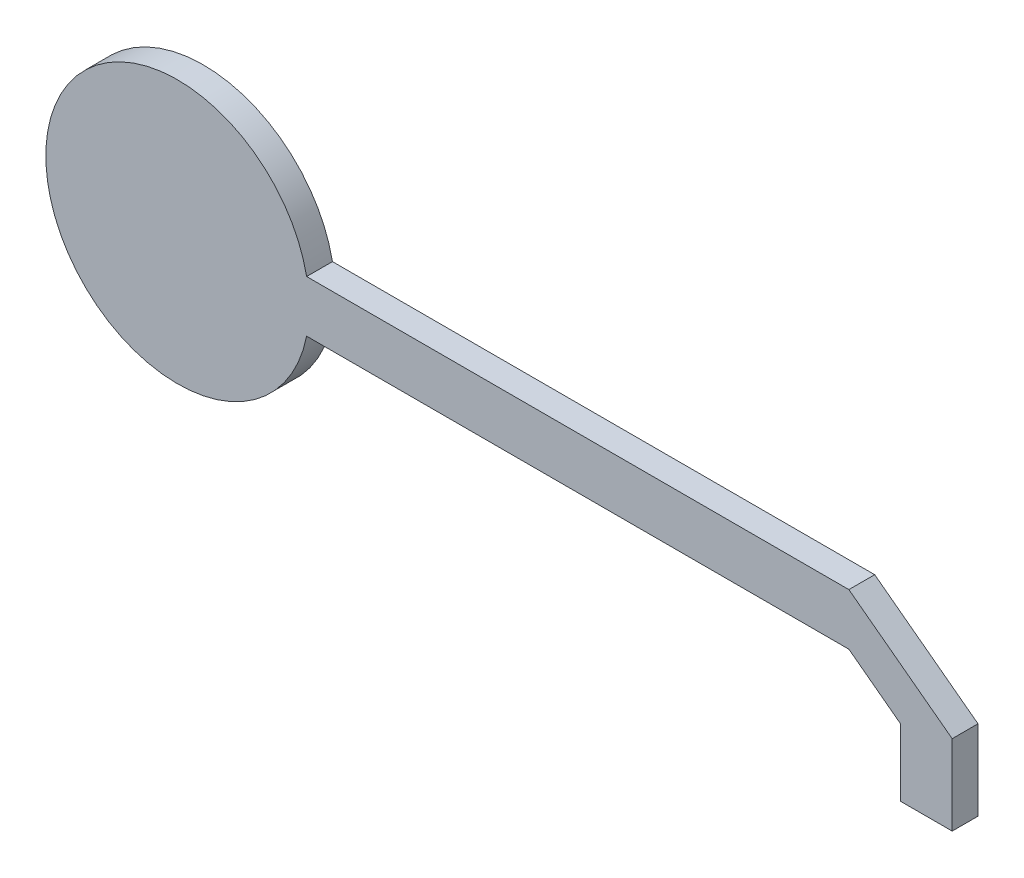
SolidWorks part; units mm, degrees
ref_plane "Alzado" through (0, 0, 0) normal (0, 0, 1) x (1, 0, 0)
ref_plane "Planta" through (0, 0, 0) normal (0, 1, 0) x (1, 0, 0)
ref_plane "Vista lateral" through (0, 0, 0) normal (1, 0, 0) x (0, 0, -1)
sketch "Croquis1" plane through (0, 0, 0) normal (0, 0, 1) x (1, 0, 0)
  line L0 (133.8574, 0) -> (1136.4137, 0) construction
  line L1 (-52.4975, 5) -> (52.4975, 5)
  line L2 (62.4975, -25.5) -> (72.4975, -25.5)
  line L3 (72.4975, -25.5) -> (72.4975, -10)
  line L4 (72.4975, -10) -> (52.4975, 5)
  line L5 (52.4975, -5) -> (62.4975, -12.5)
  line L6 (62.4975, -25.5) -> (62.4975, -12.5)
  line L7 (52.4975, -5) -> (-52.4975, -5)
  line L10 (-52.4975, 5) -> (52.4975, -5) construction
  arc A0 (-52.4975, 5) -> (-52.4975, -5) centre (-77.5025, 0) ccw
  point P10 (72.4975, -17.75)
  point P15 (0, 0)
  dimension "D1" = 51
  dimension "D2" = 5
  dimension "D3" = 150
  dimension "D4" = 10
  dimension "D5" = 10
  dimension "D6" = 25
extrude "Saliente-Extruir1" add sketch "Croquis1" along normal blind 5
sketch "Croquis3" plane through (0, 0, 0) normal (0, 0, -1) x (-1, 0, 0)
  circle A1 centre (77.5025, 0) radius 12.5 construction
  circle A2 centre (77.5025, 12.5) radius 2.5
  dimension "D1" = 25
  dimension "D3" = 5
extrude "Saliente-Extruir3" add sketch "Croquis3" along normal blind 5
sketch "Croquis4" plane through (0, 0, 0) normal (0, 0, -1) x (-1, 0, 0)
  circle A0 centre (77.5025, 0) radius 5
  dimension "D1" = 10
extrude "Saliente-Extruir4" add sketch "Croquis4" along normal blind 10
